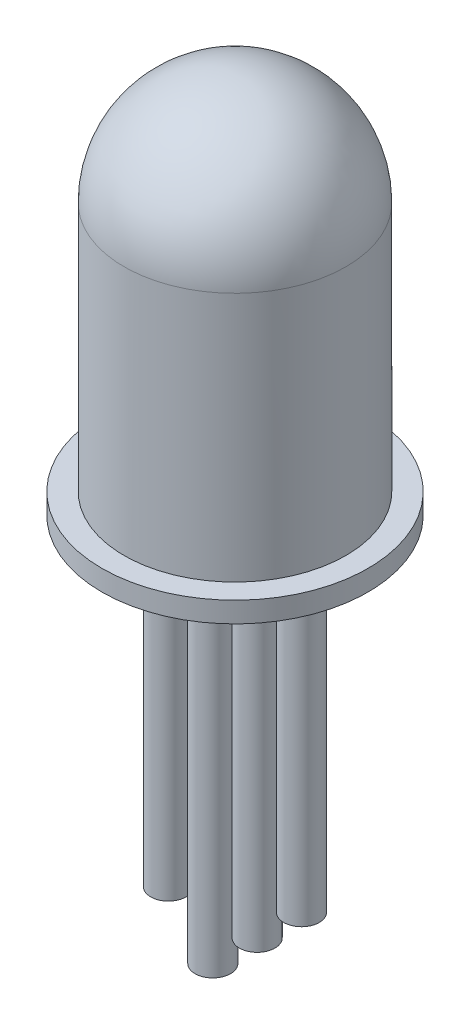
SolidWorks part; units mm, degrees
ref_plane "Plano frontal" through (0, 0, 0) normal (0, 0, 1) x (1, 0, 0)
ref_plane "Plano superior" through (0, 0, 0) normal (0, 1, 0) x (1, 0, 0)
ref_plane "Plano direito" through (0, 0, 0) normal (1, 0, 0) x (0, 0, -1)
sketch "Esboço1" plane through (0, 0, 0) normal (0, 0, 1) x (1, 0, 0)
  line L0 (0, 1.0339) -> (0, 9.6339)
  line L1 (0, 7.1339) -> (2.5, 7.1339)
  line L3 (0, 1.0339) -> (2.5, 1.0339)
  line L4 (2.5, 7.1339) -> (2.5, 1.0339)
  line L8 (3, 1.0339) -> (3, 1.497)
  line L9 (0, 1.497) -> (3, 1.497)
  line L10 (0, 1.0339) -> (3, 1.0339)
  line L11 (0, 9.6339) -> (0, 1.0339)
  arc A0 (0, 4.6339) -> (0, 9.6339) centre (0, 7.1339) ccw
  dimension "D1" = 6.1
  dimension "D2" = 5
revolve "Revolução1" add sketch "Esboço1" angle 360 about L0
sketch "Esboço2" plane through (0, 1.0339, 0) normal (0, -1, 0) x (1, 0, 0)
  circle A1 centre (-1.5, 0) radius 0.4
  circle A2 centre (-0.5, 0) radius 0.4
  circle A3 centre (0.5, 0) radius 0.4
  circle A4 centre (1.5, 0) radius 0.4
  dimension "D5" = 0.8
  dimension "D6" = 0.8
  dimension "D7" = 0.8
  dimension "D8" = 0.8
  dimension "D1" = 0.5
  dimension "D2" = 0.5
  dimension "D3" = 1
  dimension "D4" = 1
extrude "Ressalto-extrusão1" add sketch "Esboço2" along normal blind 7
sketch "Esboço3" plane through (0, -5.9661, 0) normal (0, -1, 0) x (1, 0, 0)
  circle A0 centre (0.5, 0) radius 0.4 construction
  circle A1 centre (-1.5, 0) radius 0.4 construction
  circle A2 centre (0.5, 0) radius 0.4
  circle A3 centre (-1.5, 0) radius 0.4
extrude "Ressalto-extrusão2" add sketch "Esboço3" along normal blind 1
sketch "Esboço4" plane through (0, -5.9661, 0) normal (0, -1, 0) x (1, 0, 0)
  circle A1 centre (-0.5, 0) radius 0.4
  circle A2 centre (-0.5, 0) radius 0.4
  dimension "D1" = 0
extrude "Ressalto-extrusão3" add sketch "Esboço4" along normal blind 2
